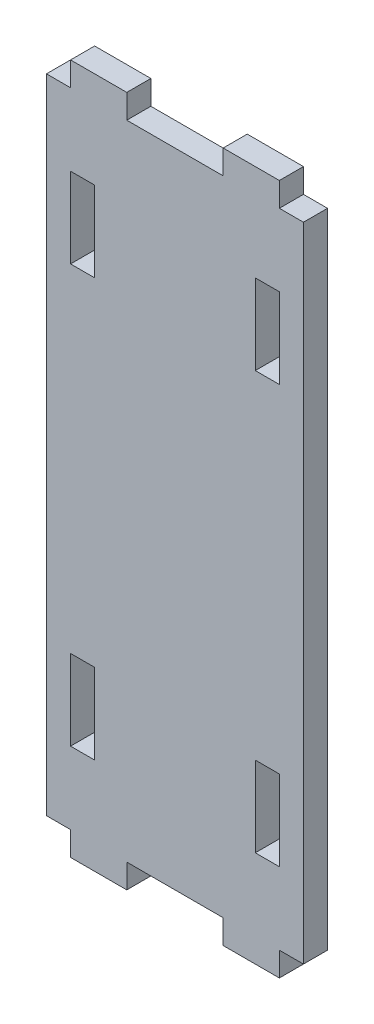
SolidWorks part; units mm, degrees
ref_plane "정면" through (0, 0, 0) normal (0, 0, 1) x (1, 0, 0)
ref_plane "윗면" through (0, 0, 0) normal (0, 1, 0) x (1, 0, 0)
ref_plane "우측면" through (0, 0, 0) normal (1, 0, 0) x (0, 0, -1)
sketch "스케치1" plane through (0, 0, 0) normal (0, 0, 1) x (1, 0, 0)
  line L1 (0, 0) -> (32, 0)
  line L2 (0, 0) -> (0, 86)
  line L3 (0, 86) -> (32, 86)
  line L4 (32, 0) -> (32, 86)
  dimension "D1" = 32
  dimension "D2" = 86
extrude "보스-돌출1" add sketch "스케치1" along normal blind 3
sketch "스케치2" plane through (0, 0, 3) normal (0, 0, 1) x (1, 0, 0)
  line L0 (32, 0) -> (32, 86) construction
  line L1 (0, 0) -> (32, 0)
  line L2 (0, 0) -> (0, 3)
  line L3 (0, 3) -> (3, 3)
  line L4 (32, 0) -> (32, 3)
  line L5 (10, 3) -> (22, 3)
  line L7 (3, 3) -> (3, 0)
  line L8 (3, 0) -> (10, 0)
  line L9 (10, 3) -> (10, 0)
  line L11 (22, 3) -> (22, 0)
  line L12 (22, 0) -> (29, 0)
  line L13 (29, 3) -> (29, 0)
  line L14 (29, 3) -> (32, 3)
  line L15 (-8.1831, 43) -> (37.0217, 43) construction
  line L16 (29, 83) -> (32, 83)
  line L17 (29, 83) -> (29, 86)
  line L18 (22, 83) -> (22, 86)
  line L19 (10, 83) -> (22, 83)
  line L20 (10, 83) -> (10, 86)
  line L21 (3, 83) -> (3, 86)
  line L22 (0, 86) -> (32, 86)
  line L23 (0, 86) -> (0, 83)
  line L24 (0, 83) -> (3, 83)
  line M9 (0, 86) -> (0, 0)
  line M10 (0, 0) -> (32, 0)
  line M11 (32, 0) -> (32, 86)
  line M12 (32, 86) -> (0, 86)
  dimension "D1" = 3
  dimension "D2" = 3
  dimension "D3" = 7
  dimension "D4" = 3
  dimension "D5" = 7
  dimension "D6" = 43
extrude "컷-돌출1" cut sketch "스케치2" against normal through all contours L20 L19 L18 M12 | L24 L21 M9 M12 | L17 L16 M11 M12 | L11 L5 L9 M10 | L7 L3 M9 M10 | L14 L13 M10 M11
sketch "스케치3" plane through (0, 0, 3) normal (0, 0, 1) x (1, 0, 0)
  line L0 (-10.6743, 43) -> (41.9059, 43) construction
  line L1 (29, 74) -> (26, 74)
  line L2 (29, 74) -> (29, 64)
  line L3 (29, 64) -> (26, 64)
  line L4 (26, 74) -> (26, 64)
  line L6 (16, 88.7196) -> (16, -3.1587) construction
  line L7 (3, 64) -> (6, 64)
  line L8 (6, 74) -> (6, 64)
  line L9 (3, 74) -> (6, 74)
  line L10 (3, 74) -> (3, 64)
  line L11 (29, 22) -> (26, 22)
  line L12 (26, 12) -> (26, 22)
  line L13 (29, 12) -> (26, 12)
  line L14 (29, 12) -> (29, 22)
  line L15 (3, 12) -> (3, 22)
  line L16 (3, 12) -> (6, 12)
  line L17 (6, 12) -> (6, 22)
  line L18 (3, 22) -> (6, 22)
  point P6 (0, 0)
  dimension "D1" = 3
  dimension "D2" = 9
  dimension "D3" = 10
extrude "컷-돌출2" cut sketch "스케치3" against normal through all
